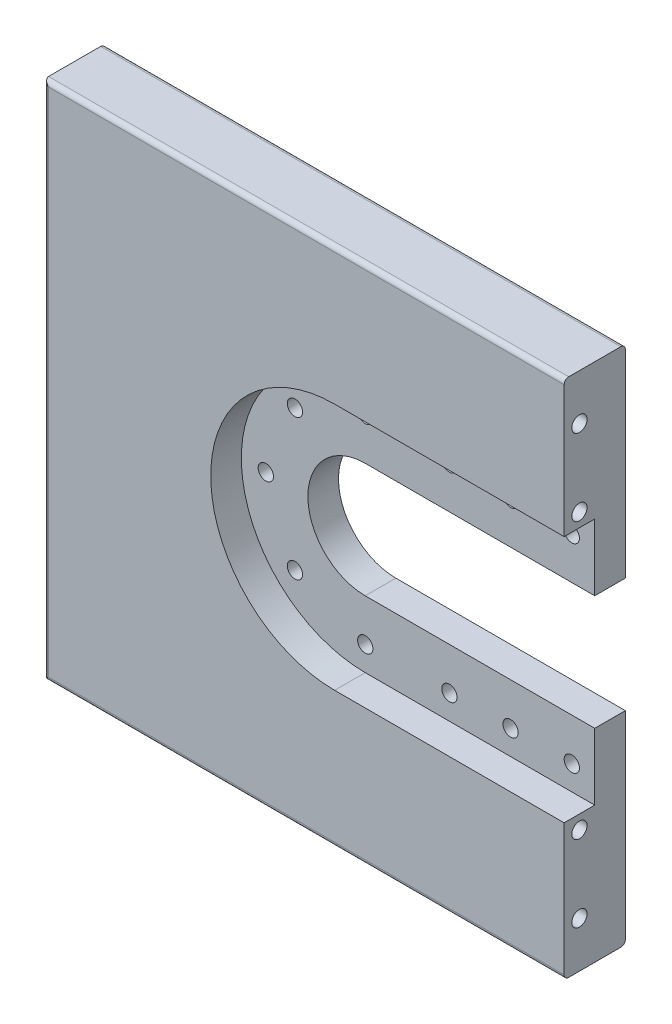
SolidWorks part; units mm, degrees
ref_plane "Front Plane" through (0, 0, 0) normal (0, 0, 1) x (1, 0, 0)
ref_plane "Top Plane" through (0, 0, 0) normal (0, 1, 0) x (1, 0, 0)
ref_plane "Right Plane" through (0, 0, 0) normal (1, 0, 0) x (0, 0, -1)
sketch "Sketch2" plane through (0, 0, 0) normal (0, 0, 1) x (1, 0, 0)
  line L0 (170, 0) -> (-170, 0)
  line L1 (-170, 0) -> (-170, 340)
  line L2 (-170, 340) -> (170, 340)
  line L3 (170, 340) -> (170, 0)
  point P4 (0, 0)
  dimension "D1" = 340
  dimension "D2" = 340
extrude "Boss-Extrude1" add sketch "Sketch2" against normal blind 40
sketch "Sketch3" plane through (0, 0, 0) normal (0, 0, 1) x (1, 0, 0)
  line L0 (170, 340) -> (170, 251)
  line L1 (170, 0) -> (170, 340) construction
  line L2 (170, 0) -> (170, 89)
  line L3 (170, 89) -> (20, 89)
  line L5 (20, 251) -> (170, 251)
  line L6 (170, 89) -> (170, 132.5)
  line L7 (20, 207.5) -> (170, 207.5)
  line L8 (20, 132.5) -> (170, 132.5)
  line L9 (170, 132.5) -> (170, 89)
  line L10 (170, 251) -> (170, 207.5)
  line L11 (170, 207.5) -> (170, 251)
  arc A0 (20, 251) -> (20, 89) centre (20, 170) ccw
  arc A1 (20, 207.5) -> (20, 132.5) centre (20, 170) ccw
  dimension "D4" = 81
  dimension "D5" = 75
  dimension "D1" = 89
  dimension "D2" = 89
  dimension "D3" = 150
extrude "Cut-Extrude1" cut sketch "Sketch3" against normal blind 20 contours A1 L7 L10 L5 A0 L3 L6 L8
sketch "Sketch4" plane through (0, 0, 0) normal (0, 0, 1) x (1, 0, 0)
  line L0 (170, 132.5) -> (170, 207.5) construction
  line L1 (20, 207.5) -> (170, 207.5) construction
  line L2 (20, 132.5) -> (170, 132.5) construction
  line L3 (170, 132.5) -> (170, 207.5)
  line L4 (20, 207.5) -> (170, 207.5)
  line L5 (20, 132.5) -> (170, 132.5)
  arc A0 (20, 207.5) -> (20, 132.5) centre (20, 170) ccw construction
  arc A1 (20, 207.5) -> (20, 132.5) centre (20, 170) ccw
extrude "Cut-Extrude2" cut sketch "Sketch4" against normal blind 199 and the other way blind 100
sketch "Sketch5" plane through (0, 0, 0) normal (0, 0, 1) x (1, 0, 0)
  line L0 (170, 251) -> (20, 251)
  line L1 (20, 251) -> (20, 235)
  line L2 (20, 89) -> (170, 89)
  line L3 (170, 89) -> (170, 251)
  line L4 (170, 105) -> (170, 235)
  line L5 (170, 235) -> (20, 235) construction
  line L6 (20, 235) -> (170, 235) construction
  line L7 (170, 235) -> (170, 105) construction
  line L8 (170, 105) -> (20, 105) construction
  line L9 (20, 105) -> (20, 89)
  line L10 (20, 235) -> (75, 235) construction
  line L11 (20, 235) -> (20, 105) construction
  line L12 (75, 235) -> (115, 235) construction
  line L13 (75, 235) -> (75, 105) construction
  line L14 (20, 170) -> (-170, 170) construction
  line L15 (-170, 340) -> (-170, 0) construction
  line L16 (20, 170) -> (20, 235) construction
  line L17 (20, 170) -> (-25.9619, 215.9619) construction
  arc A0 (20, 235) -> (20, 105) centre (20, 170) ccw construction
  circle A1 centre (20, 235) radius 5
  circle A2 centre (75, 235) radius 5
  circle A3 centre (75, 105) radius 5
  circle A4 centre (20, 105) radius 5
  circle A5 centre (115, 235) radius 5
  circle A6 centre (155, 235) radius 5
  circle A7 centre (115, 105) radius 5
  circle A8 centre (155, 105) radius 5
  circle A9 centre (75, 105) radius 5
  circle A10 centre (-25.9619, 215.9619) radius 5
  circle A11 centre (-45, 170) radius 5
  circle A12 centre (-25.9619, 124.0381) radius 5
  circle A13 centre (20, 105) radius 5
  point P11 (170, 170)
  dimension "D3" = 10
  dimension "D4" = 2
  dimension "D1" = 130
  dimension "D2" = 65
  dimension "D6" = 90
  dimension "D9" = 90
  dimension "D11" = 45
  dimension "D12" = 65
  dimension "D5" = 2
  dimension "D7" = 3
  dimension "D8" = 2
  dimension "D10" = 5
extrude "Cut-Extrude4" cut sketch "Sketch5" against normal blind 260 and the other way blind 363
ref_plane "End scree tree" through (170, 0, 0) normal (1, 0, 0) x (0, 0, -1)
sketch "Sketch6" plane through (170, 0, 0) normal (1, 0, 0) x (0, 0, -1)
  line L0 (40, 170) -> (40, 260) construction
  line L1 (40, 132.5) -> (40, 207.5) construction
  line L2 (40, 207.5) -> (40, 340) construction
  line L3 (40, 170) -> (40, 80)
  line L6 (40, 0) -> (40, 132.5) construction
  line L8 (40, 80) -> (0, 80) construction
  line L9 (0, 0) -> (0, 89) construction
  line L10 (40, 260) -> (0, 260) construction
  line L11 (0, 251) -> (0, 340) construction
  line L12 (0, 260) -> (10, 260) construction
  circle A5 centre (10, 260) radius 5
  circle A6 centre (10, 310) radius 5
  circle A7 centre (10, 80) radius 5
  circle A8 centre (10, 30) radius 5
  point P3 (40, 202.4503)
  point P4 (40, 202.4503)
  point P19 (0, 0)
  point P20 (0, 0)
  point P21 (0, 0)
  dimension "D6" = 2
  dimension "D3" = 10
  dimension "D4" = 10
  dimension "D1" = 90
  dimension "D2" = 90
  dimension "D5" = 2
extrude "Cut-Extrude5" cut sketch "Sketch6" against normal blind 18 contours A7 | A6 | A5 | A8
fillet "Fillet1" radius 3 6 edges at (-170, 170, -40) (-170, 170, 0) (0, 0, 0) (0, 0, -40) (0, 340, -40) (0, 340, 0)
